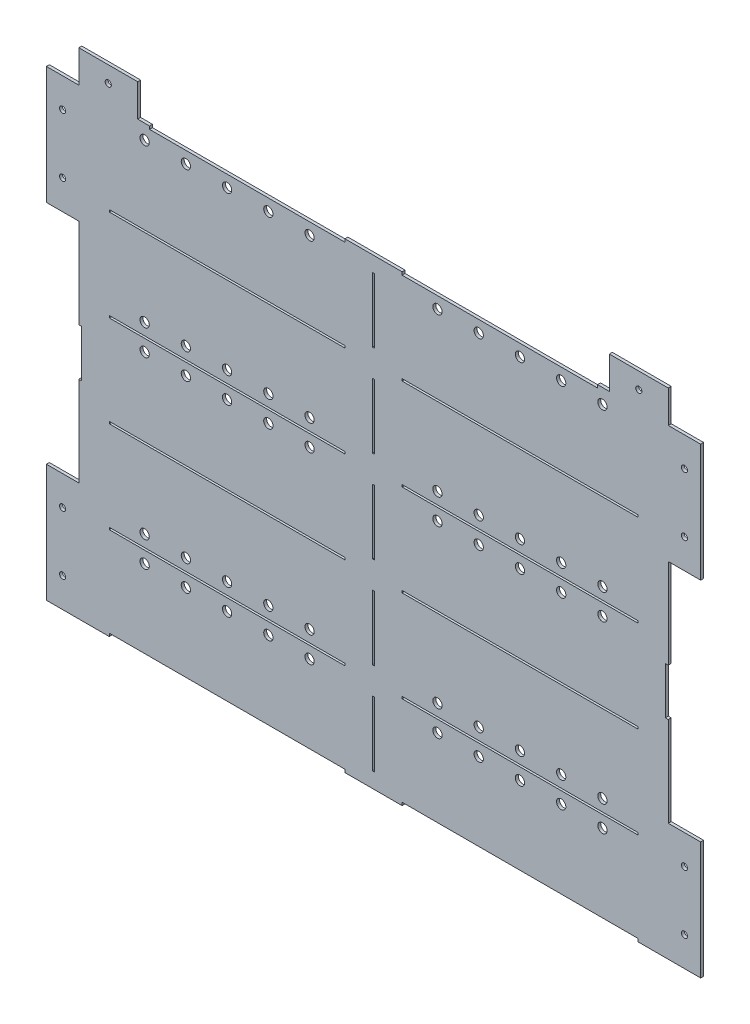
SolidWorks part; units mm, degrees
material "6061-T6 (SS)"
ref_plane "X-Y Datum" through (0, 0, 0) normal (0, 0, 1) x (1, 0, 0)
ref_plane "X-Z Datum" through (0, 0, 0) normal (0, 1, 0) x (1, 0, 0)
ref_plane "Y-Z Datum" through (0, 0, 0) normal (1, 0, 0) x (0, 0, -1)
sketch "Master Sketch" plane through (0, 0, 0) normal (0, 0, 1) x (1, 0, 0)
  line L0 (1.143, 50.5714) -> (314.5028, 50.5714) construction
  line L1 (-317.6778, 249.174) -> (317.6778, 249.174)
  line L2 (-317.6778, 249.174) -> (-317.6778, -249.174)
  line L3 (-317.6778, -249.174) -> (317.6778, -249.174)
  line L4 (317.6778, 249.174) -> (317.6778, -249.174)
  line L5 (-317.6778, 249.174) -> (317.6778, -249.174) construction
  line L6 (-317.6778, -249.174) -> (317.6778, 249.174) construction
  line L7 (-1.143, 249.174) -> (1.143, 249.174) construction
  line L8 (-1.143, 249.174) -> (-1.143, -249.174) construction
  line L9 (-1.143, -249.174) -> (1.143, -249.174) construction
  line L10 (1.143, 249.174) -> (1.143, -249.174) construction
  line L11 (-1.143, 249.174) -> (1.143, -249.174) construction
  line L12 (-1.143, -249.174) -> (1.143, 249.174) construction
  line L13 (1.143, 245.999) -> (314.5028, 245.999) construction
  line L14 (1.143, 245.999) -> (1.143, 149.4282) construction
  line L15 (1.143, 149.4282) -> (314.5028, 149.4282) construction
  line L16 (314.5028, 245.999) -> (314.5028, 149.4282) construction
  line L17 (1.143, 245.999) -> (314.5028, 149.4282) construction
  line L18 (1.143, 149.4282) -> (314.5028, 245.999) construction
  line L19 (1.143, 147.1422) -> (314.5028, 147.1422) construction
  line L20 (314.5028, 147.1422) -> (314.5028, 50.5714) construction
  line L21 (1.143, 147.1422) -> (1.143, 50.5714) construction
  line L22 (1.143, -48.2854) -> (314.5028, -48.2854) construction
  line L23 (1.143, 48.2854) -> (314.5028, 48.2854) construction
  line L24 (314.5028, 48.2854) -> (314.5028, -48.2854) construction
  line L25 (1.143, 48.2854) -> (1.143, -48.2854) construction
  line L26 (1.143, -147.1422) -> (314.5028, -147.1422) construction
  line L27 (1.143, -50.5714) -> (314.5028, -50.5714) construction
  line L28 (314.5028, -50.5714) -> (314.5028, -147.1422) construction
  line L29 (1.143, -50.5714) -> (1.143, -147.1422) construction
  line L30 (1.143, -245.999) -> (314.5028, -245.999) construction
  line L31 (1.143, -149.4282) -> (314.5028, -149.4282) construction
  line L32 (314.5028, -149.4282) -> (314.5028, -245.999) construction
  line L33 (1.143, -149.4282) -> (1.143, -245.999) construction
  line L34 (0, 249.174) -> (0, -249.174) construction
  line L35 (-1.143, -149.4282) -> (-1.143, -245.999) construction
  line L36 (-314.5028, -149.4282) -> (-314.5028, -245.999) construction
  line L37 (-1.143, -149.4282) -> (-314.5028, -149.4282) construction
  line L38 (-1.143, -245.999) -> (-314.5028, -245.999) construction
  line L39 (-1.143, -50.5714) -> (-1.143, -147.1422) construction
  line L40 (-314.5028, -50.5714) -> (-314.5028, -147.1422) construction
  line L41 (-1.143, -50.5714) -> (-314.5028, -50.5714) construction
  line L42 (-1.143, -147.1422) -> (-314.5028, -147.1422) construction
  line L43 (-1.143, 48.2854) -> (-1.143, -48.2854) construction
  line L44 (-314.5028, 48.2854) -> (-314.5028, -48.2854) construction
  line L45 (-1.143, 48.2854) -> (-314.5028, 48.2854) construction
  line L46 (-1.143, -48.2854) -> (-314.5028, -48.2854) construction
  line L47 (-1.143, 147.1422) -> (-1.143, 50.5714) construction
  line L48 (-314.5028, 147.1422) -> (-314.5028, 50.5714) construction
  line L49 (-1.143, 147.1422) -> (-314.5028, 147.1422) construction
  line L50 (-1.143, 149.4282) -> (-314.5028, 245.999) construction
  line L51 (-1.143, 245.999) -> (-314.5028, 149.4282) construction
  line L52 (-314.5028, 245.999) -> (-314.5028, 149.4282) construction
  line L53 (-1.143, 149.4282) -> (-314.5028, 149.4282) construction
  line L54 (-1.143, 245.999) -> (-1.143, 149.4282) construction
  line L55 (-1.143, 245.999) -> (-314.5028, 245.999) construction
  line L56 (-1.143, 249.174) -> (-1.143, -249.174) construction
  line L57 (-1.143, 50.5714) -> (-314.5028, 50.5714) construction
  line L59 (2.413, -152.8699) -> (313.2328, -152.8699) construction
  line L60 (2.413, -152.8699) -> (2.413, -242.5573) construction
  line L61 (2.413, -242.5573) -> (313.2328, -242.5573) construction
  line L62 (313.2328, -152.8699) -> (313.2328, -242.5573) construction
  line L63 (2.413, -152.8699) -> (313.2328, -242.5573) construction
  line L64 (2.413, -242.5573) -> (313.2328, -152.8699) construction
  point P0 (0, 0)
  point P6 (0, 0)
  point P11 (157.8229, 197.7136)
  point P54 (-157.8229, 197.7136)
  point P55 (157.8229, -197.7136)
  point P60 (157.8229, -149.4282)
  point P61 (314.5028, -197.7136)
  point P62 (-314.5028, 98.8568)
  point P63 (-314.5028, 0)
  dimension "D1" = 3.175
  dimension "D2" = 498.348
  dimension "D3" = 2.286
  dimension "D4" = 313.3598
  dimension "D5" = 96.5708
  dimension "D6" = 3.175
  dimension "D7" = 5
  dimension "D8" = 2.286
  dimension "D9" = 89.6874
  dimension "D10" = 310.8198
  dimension "D11" = 98.8568
  dimension "D12" = 635.3556
extrude "Boss-Extrude1" add sketch "Master Sketch" along normal blind 3.175
sketch "Sketch2" plane through (0, 0, 3.175) normal (0, 0, 1) x (1, 0, 0)
  line L0 (0, 317.2302) -> (0, -317.2302) construction
  line L1 (-352.6028, -185.674) -> (-317.6778, -185.674) construction
  line L6 (-335.1403, -122.174) -> (-335.1403, -185.674) construction
  line L7 (-380.7135, 0) -> (380.7135, 0) construction
  line L8 (-335.1403, -185.674) -> (-335.1403, -153.924) construction
  line L9 (-335.1403, -122.174) -> (-335.1403, -249.174) construction
  line L10 (-317.6778, -249.174) -> (-352.6028, -249.174)
  line L11 (-317.6778, -249.174) -> (-317.6778, -122.174)
  line L12 (-317.6778, -122.174) -> (-352.6028, -122.174)
  line L13 (-352.6028, -249.174) -> (-352.6028, -122.174)
  line L14 (-335.1403, -153.924) -> (-315.5316, -153.924) construction
  circle A6 centre (-335.1403, -153.924) radius 3 construction
  circle A8 centre (-335.1403, -217.424) radius 3 construction
  point P4 (0, 0)
  point P18 (0, 0)
  dimension "D8" = 34.925
  dimension "D1" = 6
  dimension "D9" = 127
extrude "Boss-Extrude2" add sketch "Sketch2" against normal blind 3.175
hole_wizard "M6 Clearance Hole1" positions "Sketch3" profile "Sketch4" hole size "M6" standard "ANSI Metric" end condition through all
sketch "Sketch3" plane through (0, 0, 3.175) normal (0, 0, 1) x (1, 0, 0)
  point P47 (-335.1403, -217.424)
  point P50 (-335.1403, -153.924)
sketch "Sketch4" plane through (-335.1403, -217.424, 3.175) normal (1, 0, 0) x (0, -1, 0)
  line L0 (0, 0) -> (0, 3.175)
  line L1 (0, 3.175) -> (3.3, 3.175)
  line L2 (3.3, 3.175) -> (3.3, 0)
  line L5 (3.3, 0) -> (0, 0)
  line L11 (0, -6.35) -> (0, 107.95) construction
  dimension "Thru Hole Dia." = 6.6
  dimension "Thru Hole Depth" = 3.175
mirror "Mirror1" about plane through (0, 0, 0) normal (1, 0, 0) of "Boss-Extrude2", "M6 Clearance Hole1"
mirror "Mirror7" about plane through (0, 0, 0) normal (0, 1, 0) of "Mirror1", "Boss-Extrude2", "M6 Clearance Hole1"
sketch "Sketch5" plane through (0, 0, 3.175) normal (0, 0, 1) x (1, 0, 0)
  line L5 (-1.143, 232.6386) -> (1.143, 232.6386)
  line L6 (-1.143, 232.6386) -> (-1.143, 162.7886)
  line L7 (-1.143, 162.7886) -> (1.143, 162.7886)
  line L8 (1.143, 232.6386) -> (1.143, 162.7886)
  line L9 (-157.8229, 197.7136) -> (157.8229, 197.7136) construction
  line L10 (-1.143, 232.6386) -> (1.143, 162.7886) construction
  line L11 (-1.143, 162.7886) -> (1.143, 232.6386) construction
  point P0 (0, 0)
  point P1 (0, 197.7136)
  dimension "D1" = 2.286
  dimension "D2" = 69.85
extrude "Cut-Extrude1" cut sketch "Sketch5" against normal through all
pattern_linear "LPattern1" count 5 spacing 98.8568 along (0, -1, 0) of "Cut-Extrude1"
sketch "Sketch7" plane through (0, 0, 3.175) normal (0, 0, 1) x (1, 0, 0)
  line L0 (-157.8229, 149.4282) -> (-157.8229, 147.1422) construction
  line L1 (-1.143, 149.4282) -> (-314.5028, 149.4282) construction
  line L2 (-1.143, 147.1422) -> (-314.5028, 147.1422) construction
  line L3 (-157.8229, 50.5714) -> (-157.8229, 48.2854) construction
  line L4 (-284.8229, 149.4282) -> (-30.8229, 149.4282)
  line L5 (-284.8229, 149.4282) -> (-284.8229, 147.1422)
  line L6 (-284.8229, 147.1422) -> (-30.8229, 147.1422)
  line L7 (-30.8229, 149.4282) -> (-30.8229, 147.1422)
  line L8 (-284.8229, 149.4282) -> (-30.8229, 147.1422) construction
  line L9 (-284.8229, 147.1422) -> (-30.8229, 149.4282) construction
  line L10 (-1.143, 50.5714) -> (-314.5028, 50.5714) construction
  line L11 (-1.143, 48.2854) -> (-314.5028, 48.2854) construction
  point P6 (-157.8229, 148.2852)
  dimension "D1" = 2.286
  dimension "D2" = 254
extrude "Cut-Extrude3" cut sketch "Sketch7" against normal through all
pattern_linear "LPattern2" count 4 spacing 98.8568 along (0, -1, 0) of "Cut-Extrude3"
mirror "Mirror4" about plane through (0, 0, 0) normal (1, 0, 0) of "LPattern2", "Cut-Extrude3"
sketch "Sketch10" plane through (0, 0, 3.175) normal (0, 0, 1) x (1, 0, 0)
  line L0 (-317.6778, 122.174) -> (-317.6778, 249.174) construction
  line L5 (352.6028, 249.174) -> (-352.6028, 249.174) construction
  line L6 (-317.6778, 266.6365) -> (-254.1778, 266.6365) construction
  line L9 (-317.6778, 249.174) -> (-254.1778, 249.174)
  line L10 (-317.6778, 249.174) -> (-317.6778, 284.099)
  line L11 (-317.6778, 284.099) -> (-254.1778, 284.099)
  line L12 (-254.1778, 249.174) -> (-254.1778, 284.099)
  circle A4 centre (-285.9278, 266.6365) radius 3
  dimension "D1" = 6
  dimension "D4" = 34.925
  dimension "D5" = 63.5
extrude "Boss-Extrude3" add sketch "Sketch10" against normal blind 3.175
hole_wizard "M6 Clearance Hole2" positions "Sketch11" profile "Sketch12" hole size "M6" standard "ANSI Metric" end condition through all
sketch "Sketch11" plane through (0, 0, 3.175) normal (0, 0, 1) x (1, 0, 0)
  point P16 (-285.9278, 266.6365)
sketch "Sketch12" plane through (-285.9278, 266.6365, 3.175) normal (1, 0, 0) x (0, -1, 0)
  line L0 (0, 0) -> (0, 3.175)
  line L1 (0, 3.175) -> (3.3, 3.175)
  line L2 (3.3, 3.175) -> (3.3, 0)
  line L5 (3.3, 0) -> (0, 0)
  line L11 (0, -6.35) -> (0, 107.95) construction
  dimension "Thru Hole Dia." = 6.6
  dimension "Thru Hole Depth" = 3.175
mirror "Mirror6" about plane through (0, 0, 0) normal (1, 0, 0) of "M6 Clearance Hole2", "Boss-Extrude3"
sketch "Sketch6" plane through (0, 0, 3.175) normal (0, 0, 1) x (1, 0, 0)
  line L0 (-157.8229, 245.999) -> (-157.8229, 249.174) construction
  line L1 (-1.143, 245.999) -> (-314.5028, 245.999) construction
  line L2 (-317.6778, 249.174) -> (317.6778, 249.174) construction
  line L3 (0, -78.309) -> (0, 78.309) construction
  line L4 (-284.8229, 249.174) -> (-30.8229, 249.174)
  line L5 (-284.8229, 249.174) -> (-284.8229, 245.999)
  line L6 (-284.8229, 245.999) -> (-30.8229, 245.999)
  line L7 (-30.8229, 249.174) -> (-30.8229, 245.999)
  line L8 (-284.8229, 249.174) -> (-30.8229, 245.999) construction
  line L9 (-284.8229, 245.999) -> (-30.8229, 249.174) construction
  line L10 (30.8229, 249.174) -> (30.8229, 245.999)
  line L11 (284.8229, 249.174) -> (30.8229, 249.174)
  line L12 (284.8229, 245.999) -> (30.8229, 245.999)
  line L13 (284.8229, 249.174) -> (284.8229, 245.999)
  line L14 (1.7463, 0) -> (-1.7463, 0) construction
  line L15 (-284.8229, -245.999) -> (-30.8229, -249.174) construction
  line L16 (-284.8229, -249.174) -> (-30.8229, -245.999) construction
  line L17 (-157.8229, -245.999) -> (-157.8229, -249.174) construction
  line L18 (284.8229, -249.174) -> (284.8229, -245.999)
  line L19 (284.8229, -245.999) -> (30.8229, -245.999)
  line L20 (284.8229, -249.174) -> (30.8229, -249.174)
  line L21 (30.8229, -249.174) -> (30.8229, -245.999)
  line L22 (-30.8229, -249.174) -> (-30.8229, -245.999)
  line L23 (-284.8229, -245.999) -> (-30.8229, -245.999)
  line L24 (-284.8229, -249.174) -> (-284.8229, -245.999)
  line L25 (-284.8229, -249.174) -> (-30.8229, -249.174)
  line L26 (-241.4778, 245.999) -> (-241.4778, 249.174)
  line L27 (-254.1778, 249.174) -> (-254.1778, 284.099) construction
  line L28 (241.4778, 245.999) -> (241.4778, 249.174)
  point P6 (-157.8229, 247.5865)
  point P29 (-157.8229, -247.5865)
  dimension "D1" = 3.175
  dimension "D2" = 254
  dimension "D3" = 12.7
extrude "Cut-Extrude2" cut sketch "Sketch6" against normal through all
sketch "Sketch13" plane through (0, 0, 0) normal (0, 0, -1) x (-1, 0, 0)
  line L0 (352.6028, -122.174) -> (352.6028, -249.174) construction
  line L1 (254.1778, 284.099) -> (317.6778, 284.099) construction
  circle A0 centre (335.1403, -153.924) radius 3.3 construction
  circle A1 centre (285.9278, 266.6365) radius 3.3 construction
  circle A2 centre (-335.1403, -153.924) radius 3.3 construction
  circle A3 centre (-335.1403, -217.424) radius 3.3 construction
  circle A4 centre (-335.1403, 153.924) radius 3.3 construction
  circle A5 centre (-335.1403, 217.424) radius 3.3 construction
  circle A6 centre (-285.9278, 266.6365) radius 3.3 construction
  circle A7 centre (335.1403, 217.424) radius 3.3 construction
  circle A8 centre (335.1403, 153.924) radius 3.3 construction
  circle A9 centre (335.1403, -217.424) radius 3.3 construction
  point P0 (338.4403, -153.924)
  point P5 (285.9278, 269.9365)
  point P10 (-338.4403, -153.924)
  point P11 (-338.4403, -217.424)
  point P14 (-338.4403, 153.924)
  point P17 (-338.4403, 217.424)
  point P20 (-285.9278, 269.9365)
  point P23 (338.4403, 217.424)
  point P26 (338.4403, 153.924)
  point P29 (338.4403, -217.424)
  dimension "D1" = 14.1625
  dimension "D2" = 14.1625
sketch "Sketch15" plane through (0, 0, 0) normal (0, 0, -1) x (-1, 0, 0)
  line L0 (317.6778, 122.174) -> (317.6778, -122.174) construction
  line L1 (314.5028, 25.4) -> (320.8528, 25.4)
  line L2 (314.5028, 25.4) -> (314.5028, -25.4)
  line L3 (314.5028, -25.4) -> (320.8528, -25.4)
  line L4 (320.8528, 25.4) -> (320.8528, -25.4)
  line L5 (314.5028, 25.4) -> (320.8528, -25.4) construction
  line L6 (314.5028, -25.4) -> (320.8528, 25.4) construction
  point P0 (317.6778, 0)
  dimension "D1" = 6.35
  dimension "D2" = 50.8
extrude "Cut-Extrude4" cut sketch "Sketch15" against normal through all
mirror "Mirror8" about plane through (0, 0, 0) normal (1, 0, 0) of "Cut-Extrude4"
sketch "Sketch16" plane through (0, 0, 0) normal (0, 0, -1) x (-1, 0, 0)
  line L0 (-314.5028, -162.1282) -> (-1.143, -162.1282) construction
  line L3 (-1.143, -245.999) -> (-1.143, -149.4282) construction
  line L4 (-1.143, -245.999) -> (-1.143, -138.3873)
  line L5 (-314.5028, -249.174) -> (-314.5028, -192.024) construction
  line L6 (-314.5028, -249.174) -> (-314.5028, -114.4159)
  line L8 (-314.5028, -162.1282) -> (-1.143, -162.1282) construction
  line L9 (-284.8229, -149.4282) -> (-30.8229, -149.4282) construction
  circle A0 centre (-157.8229, -162.1282) radius 5
  point P0 (-157.8229, -162.1282)
  point P18 (-157.8229, -157.1282)
  dimension "D1" = 10
  dimension "D2" = 12.7
extrude "Cut-Extrude5" cut sketch "Sketch16" against normal through all contours A0
pattern_linear "LPattern3" count 3 spacing 44.45 along (1, 0, 0) count 3 spacing 44.45 along (-1, 0, 0) of "Cut-Extrude5"
mirror "Mirror9" about plane through (0, 0, 0) normal (1, 0, 0) of "LPattern3", "Cut-Extrude5"
ref_plane "Plane1" through (0, -148.2852, 0) normal (0, 1, 0) x (1, 0, 0)
mirror "Mirror10" about plane through (0, -148.2852, 0) normal (0, 1, 0) of "Mirror9", "LPattern3", "Cut-Extrude5"
pattern_linear "LPattern4" count 2 spacing 395.4272 along (0, 1, 0) of "Cut-Extrude5", "LPattern3", "Mirror9"
pattern_linear "LPattern6" count 2 spacing 197.7136 along (0, 1, 0) of "Mirror10", "Cut-Extrude5", "LPattern3", "Mirror9"
